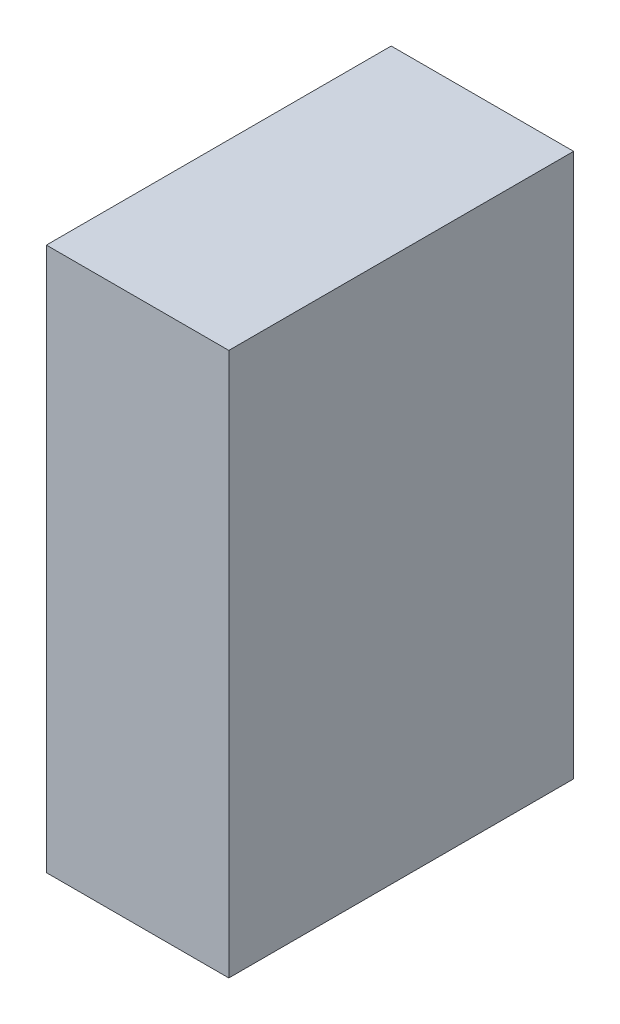
SolidWorks part; units mm, degrees
ref_plane "Front Plane" through (0, 0, 0) normal (0, 0, 1) x (1, 0, 0)
ref_plane "Top Plane" through (0, 0, 0) normal (0, 1, 0) x (1, 0, 0)
ref_plane "Right Plane" through (0, 0, 0) normal (1, 0, 0) x (0, 0, -1)
sketch "Sketch2" plane through (0, 0, 0) normal (0, 1, 0) x (1, 0, 0)
  line L1 (0, 0) -> (29.1, 0)
  line L2 (0, 0) -> (0, 55)
  line L3 (0, 55) -> (29.1, 55)
  line L4 (29.1, 0) -> (29.1, 55)
  dimension "D1" = 29.1
  dimension "D2" = 55
extrude "Boss-Extrude1" add sketch "Sketch2" along normal blind 86.7
